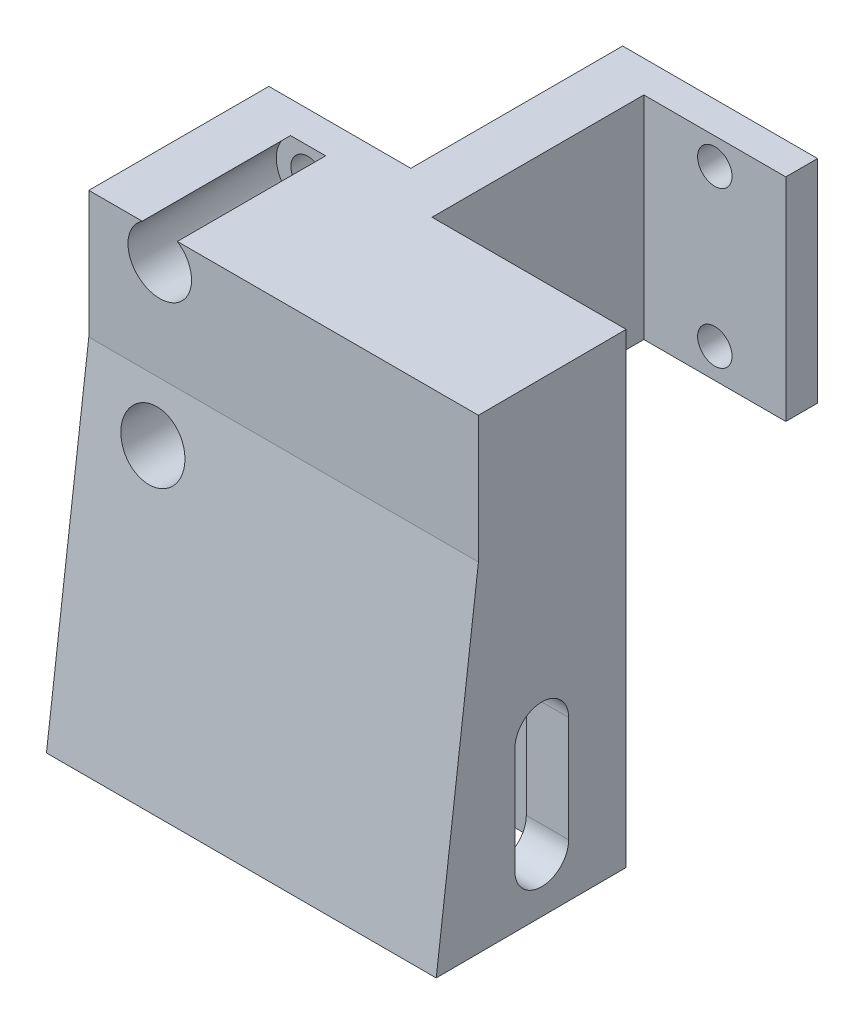
SolidWorks part; units mm, degrees
ref_plane "Front Plane" through (0, 0, 0) normal (0, 0, 1) x (1, 0, 0)
ref_plane "Top Plane" through (0, 0, 0) normal (0, 1, 0) x (1, 0, 0)
ref_plane "Right Plane" through (0, 0, 0) normal (1, 0, 0) x (0, 0, -1)
sketch "Sketch1" plane through (0, 0, 0) normal (0, 1, 0) x (1, 0, 0)
  line L0 (0, 0) -> (18.4, 0)
  line L1 (18.4, 0) -> (18.4, 20)
  line L2 (18.4, 20) -> (31.8, 20)
  line L3 (31.8, 20) -> (31.8, 23)
  line L4 (31.8, 23) -> (13.4, 23)
  line L5 (13.4, 23) -> (13.4, 3)
  line L6 (13.4, 3) -> (0, 3)
  line L7 (0, 3) -> (0, 0)
  dimension "D1" = 13.4
  dimension "D2" = 5
  dimension "D3" = 3
  dimension "D4" = 17
extrude "Boss-Extrude1" add sketch "Sketch1" along normal blind 20
sketch "Sketch2" plane through (0, 0, -20) normal (0, 0, 1) x (1, 0, 0)
  line L0 (25.1, 20) -> (25.1, 0) construction
  line L2 (18.4, 20) -> (31.8, 20) construction
  line L4 (18.4, 0) -> (31.8, 0) construction
  circle A0 centre (25.1, 17.5) radius 1.625
  circle A1 centre (25.1, 2.8) radius 1.625
  dimension "D1" = 3.25
  dimension "D2" = 2.5
  dimension "D3" = 14.7
extrude "Cut-Extrude1" cut sketch "Sketch2" against normal through all both and the other way through all
ref_plane "Plane1" through (15.9, 0, 0) normal (-1, 0, 0) x (0, 0, 1)
mirror "Mirror1" about plane through (15.9, 0, 0) normal (-1, 0, 0) of "Cut-Extrude1"
sketch "Sketch5" plane through (0, 0, 0) normal (-1, 0, 0) x (0, 0, 1)
  line L0 (0, 20) -> (0, -24)
  line L1 (0, -24) -> (18, -24)
  line L2 (18, -24) -> (14, 8)
  line L3 (14, 8) -> (14, 20)
  line L4 (14, 20) -> (0, 20)
  line L5 (-3, 0) -> (0, 0) construction
  line L6 (8, -9) -> (8, -19) construction
  line L7 (10.55, -9) -> (10.55, -19)
  line L8 (5.45, -9) -> (5.45, -19)
  arc A0 (10.55, -9) -> (5.45, -9) centre (8, -9) ccw
  arc A1 (5.45, -19) -> (10.55, -19) centre (8, -19) ccw
  point P11 (8, -14)
  dimension "D1" = 12
  dimension "D2" = 14
  dimension "D3" = 18
  dimension "D4" = 24
  dimension "D5" = 10
  dimension "D6" = 5.1
  dimension "D7" = 5
  dimension "D8" = 8
extrude "Boss-Extrude2" add sketch "Sketch5" against normal offset from surface (36.8 mm away) 5 up to face at (31.8, 10, -21.5) offset beyond the face yes
sketch "Sketch6" plane through (0, -24, 0) normal (0, -1, 0) x (1, 0, 0)
  line L3 (36.8, 18) -> (36.8, 0)
  line L4 (36.8, 18) -> (36.7309, 0)
  line L5 (36.8, 0) -> (0, 0) construction
  line L6 (36.7309, 0) -> (36.8, 0)
  dimension "D1" = 0.22
sketch "Sketch7" plane through (0, 0, 0) normal (-1, 0, 0) x (0, 0, 1)
  line L0 (14, -24) -> (14, -9)
  line L1 (0, -24) -> (18, -24) construction
  line L2 (2, -9) -> (2, -24)
  line L3 (2, -24) -> (14, -24)
  arc A0 (14, -9) -> (2, -9) centre (8, -9) ccw
  arc A1 (10.55, -9) -> (5.45, -9) centre (8, -9) ccw construction
  dimension "D1" = 12
sketch "Sketch8" plane through (0, 0, 0) normal (0, 0, -1) x (-1, 0, 0)
  circle A0 centre (-6.7, 2.8) radius 3
  circle A1 centre (-6.7, 17.5) radius 3
  dimension "D1" = 6
extrude "Cut-Extrude5" cut sketch "Sketch8" against normal through all
extrude "Cut-Extrude6" cut sketch "Sketch6" against normal through all
extrude "Cut-Extrude7" cut sketch "Sketch7" against normal offset from surface (32.7846 mm away) 4 contours L2 L3 L0 A0
